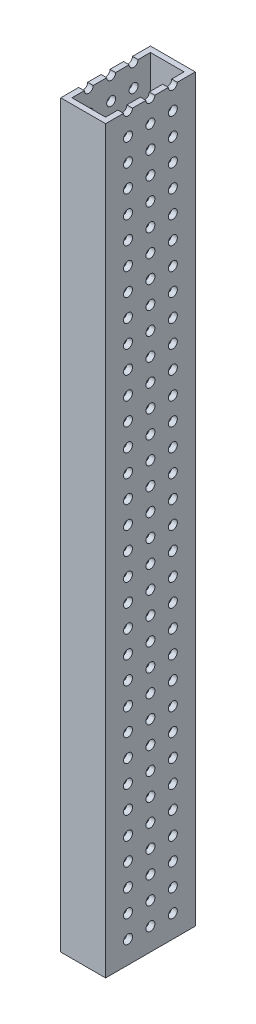
SolidWorks part; units mm, degrees
ref_plane "Front Plane" through (0, 0, 0) normal (0, 0, 1) x (1, 0, 0)
ref_plane "Top Plane" through (0, 0, 0) normal (0, 1, 0) x (1, 0, 0)
ref_plane "Right Plane" through (0, 0, 0) normal (1, 0, 0) x (0, 0, -1)
sketch "Sketch1" plane through (0, 0, 0) normal (0, 1, 0) x (1, 0, 0)
  line L0 (25.4, 50.8) -> (0, 50.8) construction
  line L1 (38.1, 50.8) -> (63.5, 50.8)
  line L2 (38.1, 50.8) -> (38.1, 0)
  line L3 (38.1, 0) -> (63.5, 0)
  line L4 (63.5, 50.8) -> (63.5, 0)
  line L5 (0, 0) -> (25.4, 0) construction
  line L6 (25.4, 0) -> (25.4, 10.16) construction
  line L7 (41.275, 47.625) -> (41.275, 3.175)
  line L8 (41.275, 3.175) -> (60.325, 3.175)
  line L9 (60.325, 47.625) -> (60.325, 3.175)
  line L10 (41.275, 47.625) -> (60.325, 47.625)
  dimension "D1" = 12.7
  dimension "D2" = 25.4
  dimension "D3" = 3.175
extrude "Boss-Extrude1" add sketch "Sketch1" along normal up to vertex contours L1 L4 L3 L2
sketch "Sketch2" plane through (63.5, 0, 0) normal (1, 0, 0) x (0, 0, -1)
  circle A0 centre (12.7, 12.7) radius 2.54 construction
  circle A1 centre (12.7, 12.7) radius 2.54
extrude "Cut-Extrude1" cut sketch "Sketch2" against normal through all
pattern_linear "LPattern1" count 33 spacing 12.7 along (0, 1, 0) count 3 spacing 12.7 along (0, 0, -1) of "Cut-Extrude1"
